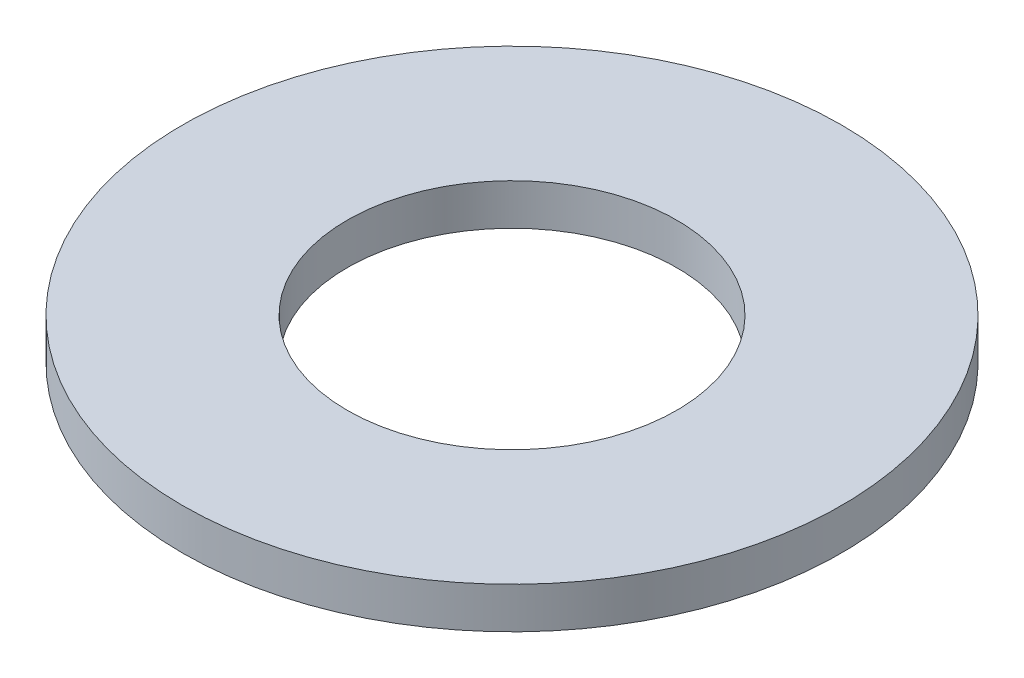
SolidWorks part; units mm, degrees
material "AISI 304"
ref_plane "前视基准面" through (0, 0, 0) normal (0, 0, 1) x (1, 0, 0)
ref_plane "上视基准面" through (0, 0, 0) normal (0, 1, 0) x (1, 0, 0)
ref_plane "右视基准面" through (0, 0, 0) normal (1, 0, 0) x (0, 0, -1)
sketch "草图1" plane through (0, 0, 0) normal (0, 1, 0) x (1, 0, 0)
  circle A0 centre (0, 0) radius 2
  circle A1 centre (0, 0) radius 4
  dimension "D1" = 4
  dimension "D2" = 8
extrude "凸台-拉伸1" add sketch "草图1" along normal blind 0.5
